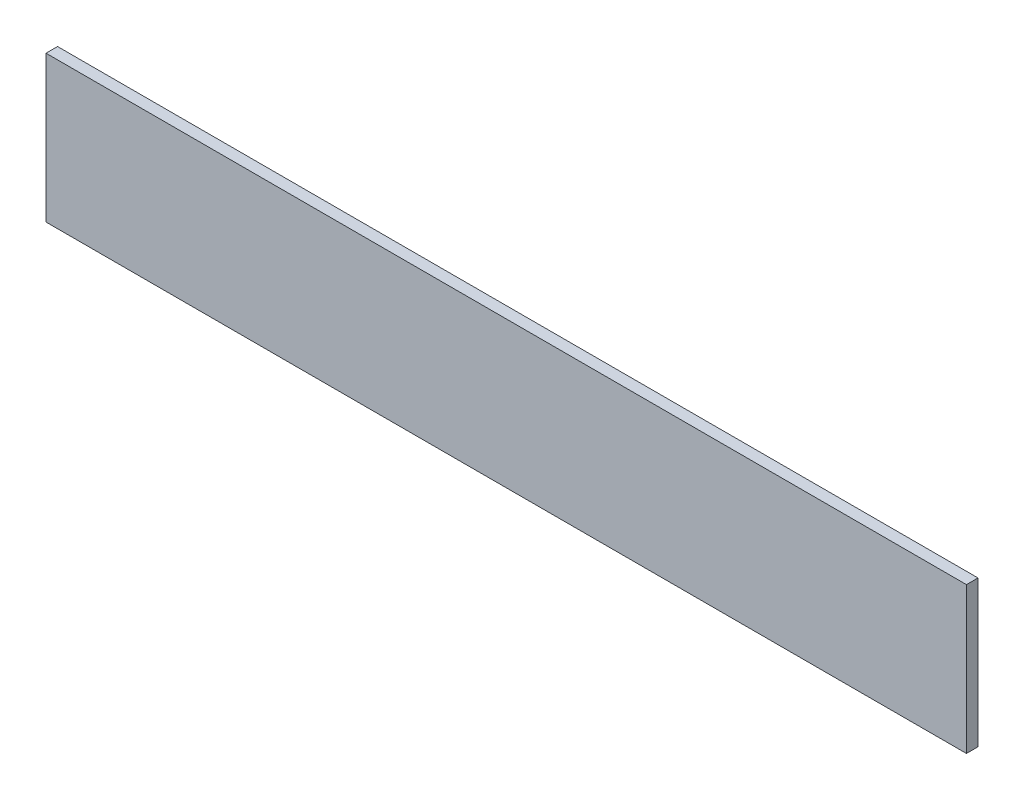
SolidWorks part; units mm, degrees
ref_plane "Front Plane" through (0, 0, 0) normal (0, 0, 1) x (1, 0, 0)
ref_plane "Top Plane" through (0, 0, 0) normal (0, 1, 0) x (1, 0, 0)
ref_plane "Right Plane" through (0, 0, 0) normal (1, 0, 0) x (0, 0, -1)
sketch "Sketch1" plane through (0, 0, 0) normal (0, 0, 1) x (1, 0, 0)
  line L1 (-16.11, 9.6729) -> (875.89, 9.6729)
  line L2 (-16.11, 9.6729) -> (-16.11, -132.0591)
  line L3 (-16.11, -132.0591) -> (875.89, -132.0591)
  line L4 (875.89, 9.6729) -> (875.89, -132.0591)
  dimension "D1" = 892
  dimension "D2" = 141.732
extrude "Boss-Extrude1" add sketch "Sketch1" against normal blind 11.2
